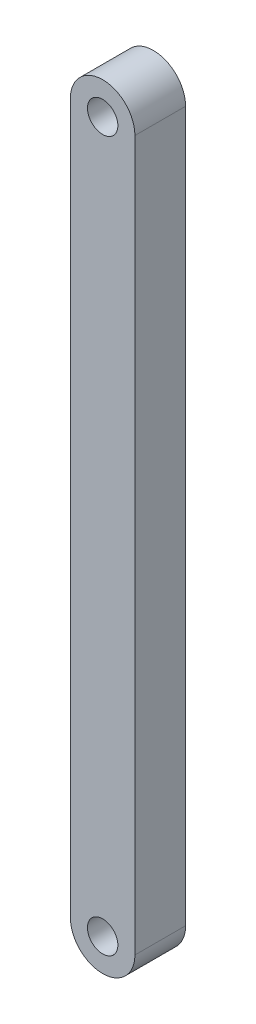
SolidWorks part; units mm, degrees
material "铸造合金钢"
ref_plane "前视基准面" through (0, 0, 0) normal (0, 0, 1) x (1, 0, 0)
ref_plane "上视基准面" through (0, 0, 0) normal (0, 1, 0) x (1, 0, 0)
ref_plane "右视基准面" through (0, 0, 0) normal (1, 0, 0) x (0, 0, -1)
sketch "草图1" plane through (0, 0, 0) normal (0, 0, 1) x (1, 0, 0)
  line L1 (-0.6364, 7) -> (0.6364, 7)
  line L2 (-0.6364, 7) -> (-0.6364, -7)
  line L3 (-0.6364, -7) -> (0.6364, -7)
  line L4 (0.6364, 7) -> (0.6364, -7)
  line L5 (-0.6364, 7) -> (0.6364, -7) construction
  line L6 (-0.6364, -7) -> (0.6364, 7) construction
  circle A0 centre (0, 7) radius 0.6364
  circle A1 centre (0, -7) radius 0.6364
  circle A2 centre (0, 7) radius 0.3
  circle A3 centre (0, -7) radius 0.3
  point P0 (0, 0)
extrude "凸台-拉伸3" add sketch "草图1" along normal blind 1 contours A2 L1 A0 | A2 L1 A0 | A1 L4 A0 L2 | A3 L3 A1 | A3 L3 A1
